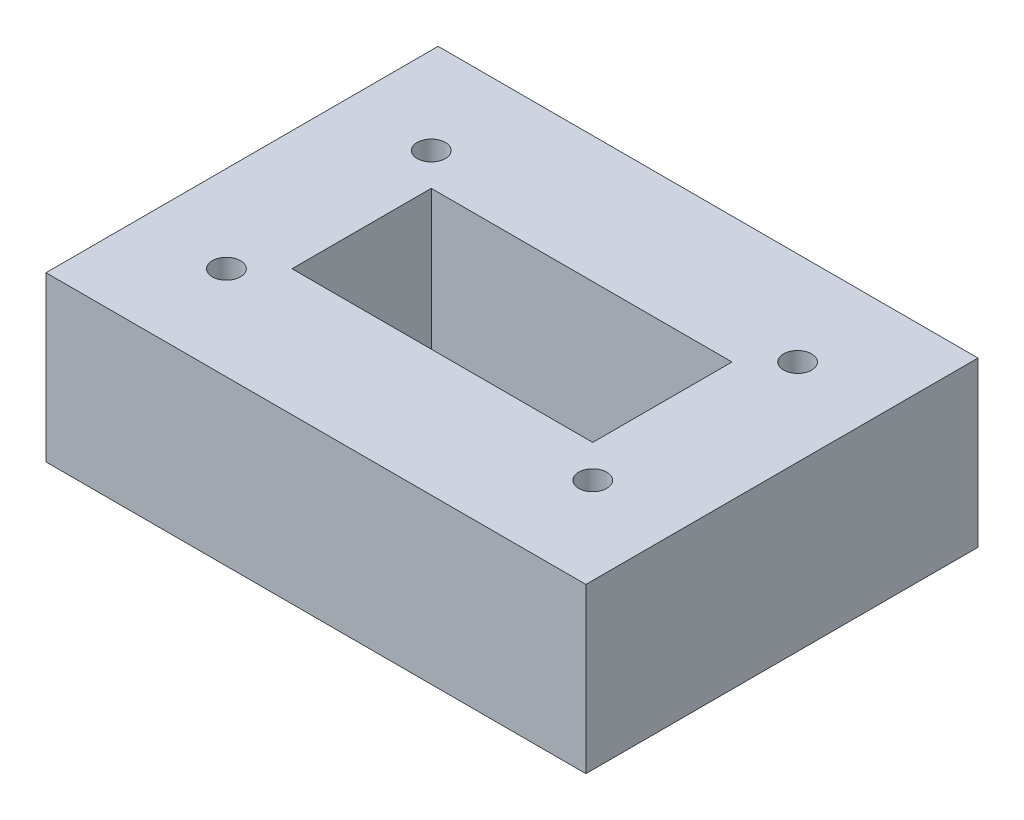
SolidWorks part; units mm, degrees
ref_plane "Front Plane" through (0, 0, 0) normal (0, 0, 1) x (1, 0, 0)
ref_plane "Top Plane" through (0, 0, 0) normal (0, 1, 0) x (1, 0, 0)
ref_plane "Right Plane" through (0, 0, 0) normal (1, 0, 0) x (0, 0, -1)
sketch "Sketch1" plane through (0, 0, 0) normal (0, 1, 0) x (1, 0, 0)
  line L0 (-111.76, 0) -> (-111.76, 9.42)
  line L1 (0, 0) -> (-111.76, 0)
  line L2 (0, 0) -> (0, 75.69)
  line L3 (0, 75.69) -> (-111.76, 75.69)
  line L4 (-111.76, 0) -> (-111.76, 9.42)
  line L5 (-111.76, 9.42) -> (-100.58, 9.42)
  line L7 (-111.76, 16.28) -> (-100.58, 16.28)
  line L8 (-111.76, 16.28) -> (-111.76, 75.69)
  line L9 (0, 0) -> (0, 37.845)
  line L10 (0, 37.845) -> (-111.76, 37.845)
  line L11 (-55.88, 75.69) -> (-55.88, 0)
  line L12 (-111.76, 66.27) -> (-100.58, 66.27)
  line L13 (-111.76, 59.41) -> (-100.58, 59.41)
  line L14 (0, 9.42) -> (-11.18, 9.42)
  line L15 (0, 16.28) -> (-11.18, 16.28)
  line L16 (0, 59.41) -> (-11.18, 59.41)
  line L17 (0, 66.27) -> (-11.18, 66.27)
  arc A0 (-100.58, 9.42) -> (-100.58, 16.28) centre (-100.58, 12.85) ccw
  arc A1 (-100.58, 66.27) -> (-100.58, 59.41) centre (-100.58, 62.84) cw
  arc A2 (-11.18, 9.42) -> (-11.18, 16.28) centre (-11.18, 12.85) cw
  arc A3 (-11.18, 66.27) -> (-11.18, 59.41) centre (-11.18, 62.84) ccw
  dimension "D1" = 111.76
  dimension "D2" = 75.69
sketch "Sketch2" plane through (0, 0, 0) normal (0, 1, 0) x (1, 0, 0)
  line L0 (-55.88, 0) -> (-55.88, 75.69)
  line L1 (-111.76, 0) -> (-121.76, 0)
  line L2 (-111.76, 0) -> (-111.76, -10)
  line L3 (-111.76, -10) -> (-121.76, -10)
  line L4 (-121.76, 0) -> (-121.76, -10)
  line L5 (0, 75.69) -> (10, 75.69)
  line L6 (0, 75.69) -> (0, 85.69)
  line L7 (0, 85.69) -> (10, 85.69)
  line L8 (10, 75.69) -> (10, 85.69)
  line L9 (-111.76, 37.845) -> (0, 37.845)
  circle A0 centre (-100.58, 12.85) radius 3.43
  circle A1 centre (-100.58, 12.85) radius 8
  circle A2 centre (-100.58, 62.84) radius 8
  circle A3 centre (-11.18, 12.85) radius 8
  circle A4 centre (-11.18, 62.84) radius 8
  dimension "D1" = 10
  dimension "D2" = 10
  dimension "D3" = 10
  dimension "D4" = 10
sketch "Sketch3" plane through (0, 0, 0) normal (0, 1, 0) x (1, 0, 0)
  line L0 (-100.58, 54.84) -> (-92.58, 54.84)
  line L1 (-121.76, -10) -> (-108.58, -10)
  line L2 (-121.76, -10) -> (-121.76, 12.85)
  line L5 (-108.58, -10) -> (-11.18, -10)
  line L9 (10, 85.69) -> (-3.18, 85.69)
  line L10 (10, 85.69) -> (10, 62.84)
  line L14 (10, 62.84) -> (10, -10)
  line L15 (10, -10) -> (-3.18, -10)
  line L19 (-11.18, -10) -> (-3.18, -10)
  line L22 (-121.76, 12.85) -> (-121.76, 62.84)
  line L26 (-121.76, 62.84) -> (-121.76, 85.69)
  line L27 (-121.76, 85.69) -> (-108.58, 85.69)
  line L29 (-108.58, 85.69) -> (-11.18, 85.69)
  line L35 (-11.18, 85.69) -> (-3.18, 85.69)
  line L37 (-92.58, 62.84) -> (-92.58, 54.84)
  line L38 (-19.18, 12.85) -> (-19.18, 20.85)
  line L39 (-11.18, 20.85) -> (-19.18, 20.85)
  line L41 (-92.58, 54.84) -> (-19.18, 54.84)
  line L42 (-92.58, 54.84) -> (-92.58, 20.85)
  line L43 (-92.58, 20.85) -> (-19.18, 20.85)
  line L44 (-19.18, 54.84) -> (-19.18, 20.85)
  circle A1 centre (-11.18, 12.85) radius 8 construction
  circle A3 centre (-100.58, 62.84) radius 8 construction
  circle A8 centre (-100.58, 62.84) radius 3.43
  circle A9 centre (-11.18, 62.84) radius 3.43
  circle A10 centre (-11.18, 12.85) radius 3.43
  circle A11 centre (-100.58, 12.85) radius 3.43
sketch "Sketch4" plane through (0, 0, 0) normal (0, 1, 0) x (1, 0, 0)
  line L0 (-108.58, 62.84) -> (-108.58, 70.84)
  line L1 (-108.58, 12.85) -> (-108.58, 4.85)
  line L2 (-108.58, 70.84) -> (-121.76, 70.84)
  line L3 (-108.58, 70.84) -> (-108.58, 85.69)
  line L4 (-108.58, 85.69) -> (-121.76, 85.69)
  line L5 (-121.76, 70.84) -> (-121.76, 85.69)
  line L6 (-55.88, 0) -> (-55.88, 75.69)
  line L7 (-108.58, 4.85) -> (-121.76, 4.85)
  line L8 (-108.58, 4.85) -> (-108.58, -10)
  line L9 (-108.58, -10) -> (-121.76, -10)
  line L10 (-121.76, 4.85) -> (-121.76, -10)
  line L11 (0, 0) -> (-111.76, 0) construction
  line L12 (10, 4.85) -> (10, -10)
  line L13 (-3.18, -10) -> (10, -10)
  line L14 (-3.18, 4.85) -> (-3.18, -10)
  line L15 (-3.18, 4.85) -> (10, 4.85)
  line L16 (-3.18, 70.84) -> (10, 70.84)
  line L17 (10, 70.84) -> (10, 85.69)
  line L18 (-3.18, 85.69) -> (10, 85.69)
  line L19 (-3.18, 70.84) -> (-3.18, 85.69)
  circle A0 centre (-100.58, 62.84) radius 8 construction
  circle A1 centre (-100.58, 12.85) radius 8 construction
sketch "Sketch8" plane through (0, 0, 0) normal (0, 1, 0) x (1, 0, 0)
  line L1 (-92.58, 20.85) -> (-19.18, 20.85)
  line L2 (-92.58, 20.85) -> (-92.58, 54.84)
  line L3 (-92.58, 54.84) -> (-19.18, 54.84)
  line L4 (-19.18, 20.85) -> (-19.18, 54.84)
  line L5 (-121.76, 85.69) -> (10, 85.69)
  line L6 (-121.76, 85.69) -> (-121.76, -10)
  line L7 (-121.76, -10) -> (10, -10)
  line L8 (10, 85.69) -> (10, -10)
  circle A0 centre (-100.58, 12.85) radius 3.43
  circle A1 centre (-100.58, 62.84) radius 3.43
  circle A2 centre (-11.18, 62.84) radius 3.43
  circle A3 centre (-11.18, 12.85) radius 3.43
extrude "Boss-Extrude4" add sketch "Sketch8" along normal blind 40
sketch "Sketch9" plane through (0, 0, 0) normal (0, -1, 0) x (1, 0, 0)
  circle A0 centre (-100.58, -12.85) radius 8
  circle A1 centre (-11.18, -12.85) radius 8
  circle A2 centre (-11.18, -62.84) radius 8
  circle A3 centre (-100.58, -62.84) radius 8
extrude "Cut-Extrude2" cut sketch "Sketch9" against normal blind 8
sketch "Sketch10" plane through (0, 0, 0) normal (0, -1, 0) x (1, 0, 0)
  line L1 (-121.76, 10) -> (10, 10)
  line L2 (-121.76, 10) -> (-121.76, 60)
  line L3 (-121.76, 60) -> (10, 60)
  line L4 (10, 10) -> (10, 60)
  line L5 (-121.76, 60) -> (-108.58, 60)
  line L6 (-121.76, 60) -> (-121.76, 45.15)
  line L7 (-121.76, 45.15) -> (-108.58, 45.15)
  line L8 (-108.58, 60) -> (-108.58, 45.15)
  dimension "D1" = 50
  dimension "D2" = 13.18
  dimension "D3" = 14.85
sketch "Sketch11" plane through (0, 40, 0) normal (0, 1, 0) x (1, 0, 0)
  line L1 (-121.76, -60) -> (10, -60)
  line L2 (-121.76, -60) -> (-121.76, -10)
  line L3 (-121.76, -10) -> (10, -10)
  line L4 (10, -60) -> (10, -10)
